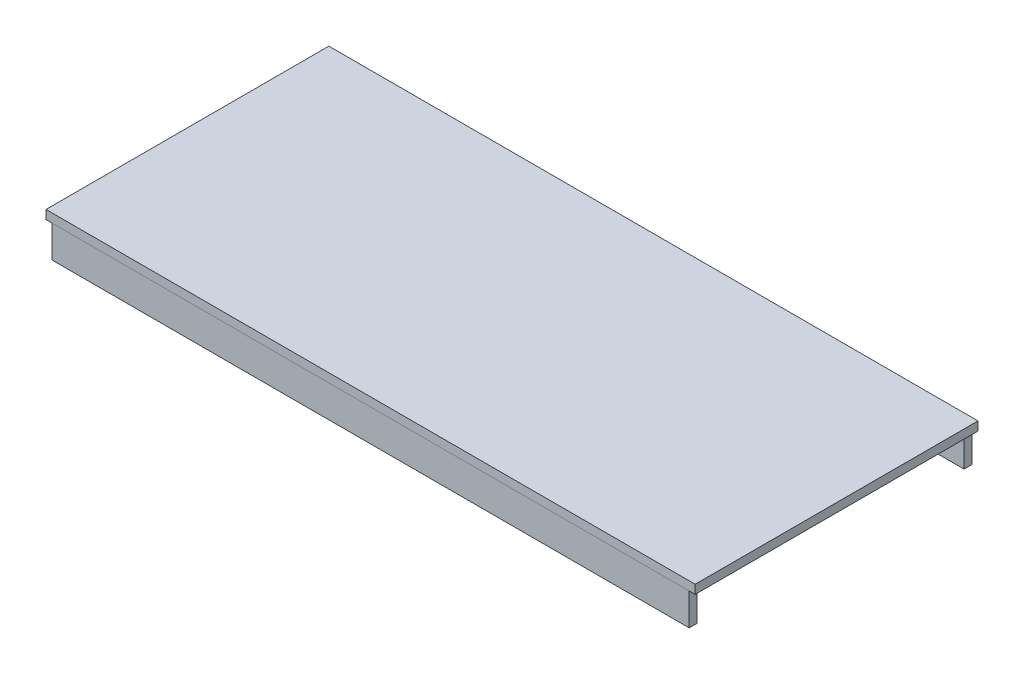
SolidWorks part; units mm, degrees
material "Pine"
ref_plane "Front Plane" through (0, 0, 0) normal (0, 0, 1) x (1, 0, 0)
ref_plane "Top Plane" through (0, 0, 0) normal (0, 1, 0) x (1, 0, 0)
ref_plane "Right Plane" through (0, 0, 0) normal (1, 0, 0) x (0, 0, -1)
sketch "Sketch1" plane through (0, 0, 0) normal (0, 1, 0) x (1, 0, 0)
  line L0 (0, -55) -> (0, 55) construction
  line L1 (-700, 305) -> (700, 305)
  line L2 (-700, 305) -> (-700, -305)
  line L3 (-700, -305) -> (700, -305)
  line L4 (700, 305) -> (700, -305)
  line L5 (-55, 0) -> (55, 0) construction
  dimension "D1" = 1400
  dimension "D2" = 610
  dimension "D3" = 700
  dimension "D4" = 305
extrude "Boss-Extrude1" add sketch "Sketch1" against normal blind 19
sketch "Sketch2" plane through (700, 0, 0) normal (1, 0, 0) x (0, 0, -1)
  line L1 (-305, -19) -> (-288, -19)
  line L2 (-305, -19) -> (-305, -88)
  line L3 (-305, -88) -> (-288, -88)
  line L4 (-288, -19) -> (-288, -88)
  line L5 (305, -19) -> (288, -19)
  line L6 (305, -19) -> (305, -88)
  line L7 (305, -88) -> (288, -88)
  line L8 (288, -19) -> (288, -88)
  dimension "D1" = 69
  dimension "D2" = 17
extrude "Boss-Extrude2" add sketch "Sketch2" against normal offset from surface (1374 mm away) 13 from offset 13 separate body up to face at (-700, -9.5, 0) offset against normal yes
